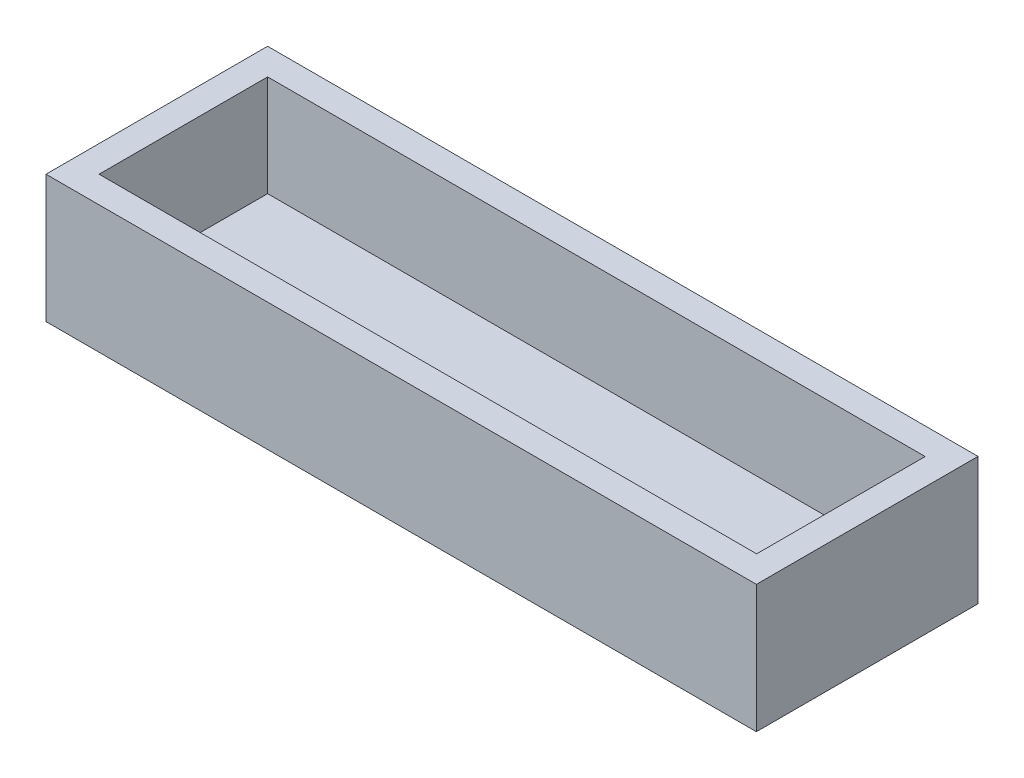
SolidWorks part; units mm, degrees
ref_plane "Front Plane" through (0, 0, 0) normal (0, 0, 1) x (1, 0, 0)
ref_plane "Top Plane" through (0, 0, 0) normal (0, 1, 0) x (1, 0, 0)
ref_plane "Right Plane" through (0, 0, 0) normal (1, 0, 0) x (0, 0, -1)
sketch "Sketch2" plane through (0, 0, 0) normal (0, 1, 0) x (1, 0, 0)
  line L1 (-133.825, 41.75) -> (133.825, 41.75)
  line L2 (-133.825, 41.75) -> (-133.825, -41.75)
  line L3 (-133.825, -41.75) -> (133.825, -41.75)
  line L4 (133.825, 41.75) -> (133.825, -41.75)
  line L5 (-133.825, 41.75) -> (133.825, -41.75) construction
  line L6 (-133.825, -41.75) -> (133.825, 41.75) construction
  point P0 (0, 0)
  dimension "D1" = 267.65
  dimension "D2" = 83.5
extrude "Boss-Extrude2" add sketch "Sketch2" along normal blind 10
sketch "Sketch3" plane through (0, 10, 0) normal (0, 1, 0) x (1, 0, 0)
  line L0 (-133.825, 41.75) -> (-123.825, 41.75) construction
  line L1 (133.825, 41.75) -> (-133.825, 41.75) construction
  line L2 (-133.825, 41.75) -> (-133.825, 31.75) construction
  line L3 (-133.825, 41.75) -> (-133.825, -41.75) construction
  line L4 (-133.825, 31.75) -> (133.825, 31.75) construction
  line L5 (133.825, -41.75) -> (133.825, 41.75) construction
  line L6 (-123.825, 41.75) -> (-123.825, -41.75) construction
  line L7 (-133.825, -41.75) -> (133.825, -41.75) construction
  line L8 (-133.825, -41.75) -> (-133.825, -31.75) construction
  line L9 (-133.825, -31.75) -> (133.825, -31.75) construction
  line L10 (133.825, 41.75) -> (123.919, 41.75)
  line L11 (-123.825, 41.75) -> (-133.825, 41.75)
  line L12 (-123.825, 41.75) -> (-123.825, -41.75)
  line L13 (-123.825, -41.75) -> (-133.825, -41.75)
  line L14 (-133.825, 41.75) -> (-133.825, -41.75)
  line L15 (133.825, 31.75) -> (-133.825, 31.75)
  line L16 (133.825, 31.75) -> (133.825, 41.75)
  line L17 (133.825, 41.75) -> (-133.825, 41.75)
  line L18 (-133.825, 31.75) -> (-133.825, 41.75)
  line L19 (133.825, -41.75) -> (-133.825, -41.75)
  line L20 (133.825, -41.75) -> (133.825, -31.75)
  line L21 (133.825, -31.75) -> (-133.825, -31.75)
  line L22 (-133.825, -41.75) -> (-133.825, -31.75)
  line L23 (123.919, 41.75) -> (123.919, -41.75)
  line M4 (133.825, -41.75) -> (133.825, 41.75)
  line M5 (133.825, 41.75) -> (-133.825, 41.75)
  line M6 (-133.825, 41.75) -> (-133.825, -41.75)
  line M7 (-133.825, -41.75) -> (133.825, -41.75)
  dimension "D1" = 10
  dimension "D2" = 10
  dimension "D3" = 10
  dimension "D4" = 9.906
extrude "Boss-Extrude3" add sketch "Sketch3" along normal blind 38.1 contours L21 L12 L15 L14 | L15 L12 M5 M6 | L15 L12 M4 M5 | L21 L12 M4 M7 | L12 L21 M6 M7 | L23 L15 M5 M4 | L15 L23 L21 M4 | L21 L23 L19 M4
sketch "Sketch9" plane through (0, 10, 0) normal (0, 1, 0) x (1, 0, 0)
  line L1 (-123.825, 31.75) -> (-117.475, 31.75)
  line L2 (-123.825, 31.75) -> (-123.825, 25.4)
  line L3 (-123.825, 25.4) -> (-117.475, 25.4)
  line L4 (-117.475, 31.75) -> (-117.475, 25.4)
  line L5 (-123.825, -31.75) -> (-117.475, -31.75)
  line L6 (-123.825, -31.75) -> (-123.825, -25.4)
  line L7 (-123.825, -25.4) -> (-117.475, -25.4)
  line L8 (-117.475, -31.75) -> (-117.475, -25.4)
  line L9 (123.919, 31.75) -> (117.569, 31.75)
  line L10 (123.919, 31.75) -> (123.919, 25.4)
  line L11 (123.919, 25.4) -> (117.569, 25.4)
  line L12 (117.569, 31.75) -> (117.569, 25.4)
  line L13 (123.919, -31.75) -> (117.569, -31.75)
  line L14 (123.919, -31.75) -> (123.919, -25.4)
  line L15 (123.919, -25.4) -> (117.569, -25.4)
  line L16 (117.569, -31.75) -> (117.569, -25.4)
  dimension "D1" = 6.35
  dimension "D2" = 6.35
  dimension "D3" = 6.35
  dimension "D4" = 6.35
  dimension "D5" = 6.35
  dimension "D6" = 6.35
  dimension "D7" = 6.35
  dimension "D8" = 6.35
